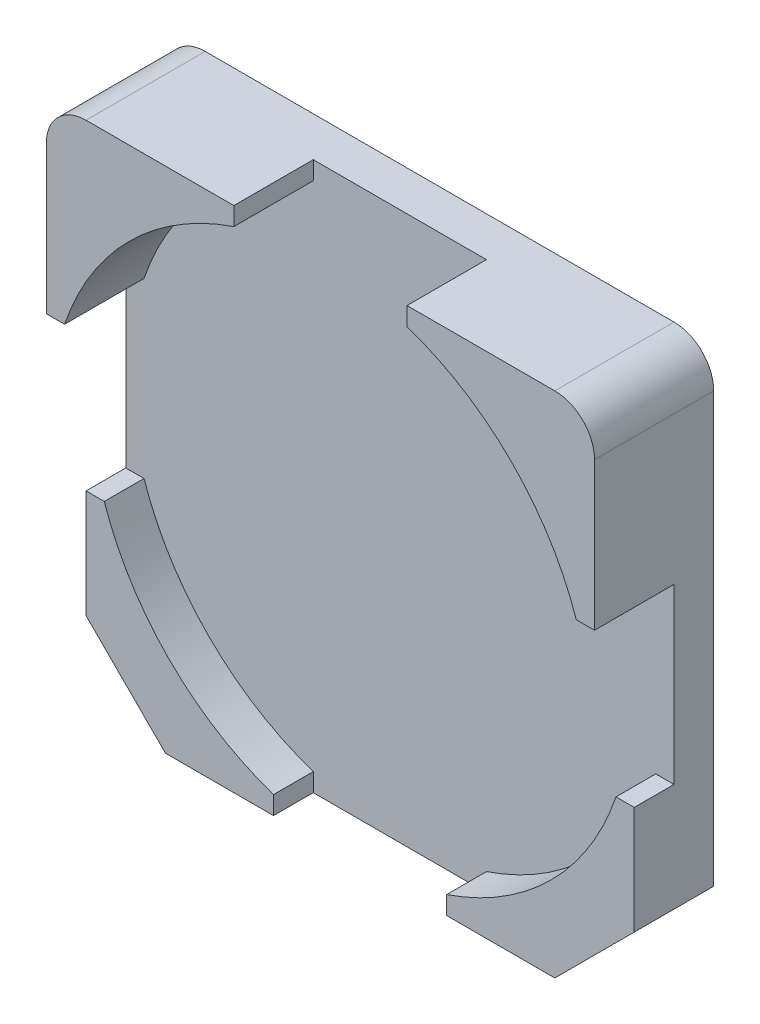
SolidWorks part; units mm, degrees
ref_plane "Plan de face" through (0, 0, 0) normal (0, 0, 1) x (1, 0, 0)
ref_plane "Plan de dessus" through (0, 0, 0) normal (0, 1, 0) x (1, 0, 0)
ref_plane "Plan de droite" through (0, 0, 0) normal (1, 0, 0) x (0, 0, -1)
sketch "Esquisse1" plane through (0, 0, 0) normal (0, 0, 1) x (1, 0, 0)
  line L1 (0, 0) -> (6.9, 0)
  line L2 (0, 0) -> (0, 6.9)
  line L3 (0, 6.9) -> (6.9, 6.9)
  line L4 (6.9, 0) -> (6.9, 6.9)
extrude "Boss.-Extru.1" add sketch "Esquisse1" along normal blind 1.5
sketch "Esquisse2" plane through (0, 0, 1.5) normal (0, 0, 1) x (1, 0, 0)
  line L0 (0, 6.9) -> (6.9, 0) construction
  line L1 (6.9, 6.9) -> (0, 0) construction
  circle A0 centre (3.45, 3.45) radius 3.4
extrude "Enlèv. mat.-Extru.7" cut sketch "Esquisse2" against normal blind 1
sketch "Esquisse3" plane through (0, 0, 1.5) normal (0, 0, 1) x (1, 0, 0)
  line L0 (0, 4.5404) -> (2.36, 4.5404)
  line L1 (0, 6.9) -> (0, 0) construction
  line L2 (6.9, 0) -> (6.9, 6.9) construction
  line L3 (0, 3.45) -> (6.9, 3.45) construction
  line L4 (0, 2.3596) -> (2.36, 2.3596)
  line L5 (0, 4.5404) -> (0, 2.3596)
  line L6 (6.9, 4.5404) -> (6.9, 2.3596)
  line L7 (3.45, 0) -> (3.45, 6.9) construction
  line L8 (0, 0) -> (6.9, 0) construction
  line L9 (6.9, 6.9) -> (0, 6.9) construction
  line L10 (4.54, 0) -> (4.54, 2.3596)
  line L11 (2.36, 0) -> (2.36, 2.3596)
  line L12 (2.36, 6.9) -> (4.54, 6.9)
  line L13 (2.36, 0) -> (4.54, 0)
  line L14 (4.54, 2.3596) -> (6.9, 2.3596)
  line L15 (2.36, 4.5404) -> (2.36, 6.9)
  line L16 (4.54, 4.5404) -> (6.9, 4.5404)
  line L17 (2.36, 0) -> (2.36, 6.9) construction
  line L18 (4.54, 4.5404) -> (4.54, 6.9)
  line L20 (4.54, 0) -> (4.54, 6.9) construction
  dimension "D1" = 1.09
  dimension "D2" = 1.09
extrude "Enlèv. mat.-Extru.8" cut sketch "Esquisse3" against normal blind 1
sketch "Esquisse4" plane through (0, 0, 1.5) normal (0, 0, 1) x (1, 0, 0)
  line L1 (6.9, 0) -> (0, 0)
  line L2 (6.9, 0) -> (6.9, 2.3596)
  line L3 (6.9, 2.3596) -> (0, 2.3596)
  line L4 (0, 0) -> (0, 2.3596)
extrude "Enlèv. mat.-Extru.9" cut sketch "Esquisse4" against normal blind 0.5
chamfer "Chanfrein1" distance 1 angle 45 2 edges at (0, 0, 0.5) (6.9, 0, 0.5)
fillet "Congé1" radius 0.5 2 edges at (6.9, 6.9, 0.75) (0, 6.9, 0.75)
